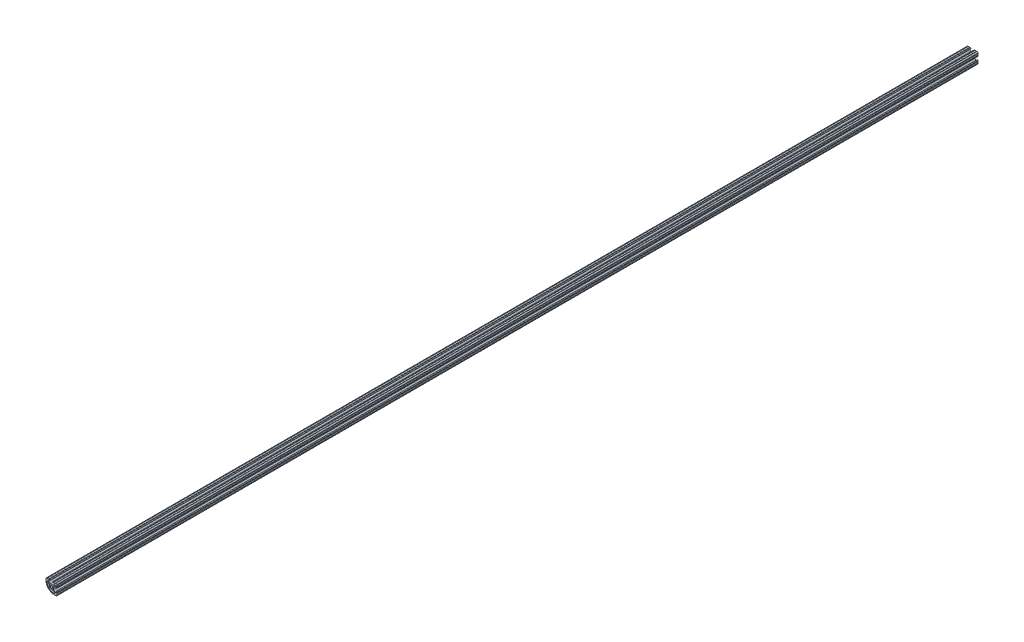
SolidWorks part; units mm, degrees
ref_plane "Front Plane" through (0, 0, 0) normal (0, 0, 1) x (1, 0, 0)
ref_plane "Top Plane" through (0, 0, 0) normal (0, 1, 0) x (1, 0, 0)
ref_plane "Right Plane" through (0, 0, 0) normal (1, 0, 0) x (0, 0, -1)
sketch "Sketch1" plane through (0, 0, 0) normal (0, 0, 1) x (1, 0, 0)
  line L0 (-5.2807, 3.6664) -> (-8.6034, 6.9891)
  line L2 (-12.7, 9.5758) -> (-12.7, 6.35)
  line L17 (1.6698, 4.4958) -> (-1.6698, 4.4958)
  line L18 (-3.9149, 5.4257) -> (-7.0932, 8.604)
  line L19 (-6.3119, 10.4902) -> (-4.3561, 10.4902)
  line L20 (-4.3561, 12.7) -> (-5.334, 12.7)
  line L21 (-6.35, 12.7) -> (-9.5758, 12.7)
  line L22 (-12.7, -12.7) -> (12.7, 12.7) construction
  line L23 (0, 12.7) -> (0, -12.7) construction
  line L24 (-12.7, -12.7) -> (12.7, -12.7) construction
  line L25 (-7.1204, -7.1204) -> (-1.5408, -12.7) construction
  line L26 (-12.0825, 12.0825) -> (0, 0) construction
  line L27 (3.9149, 5.4257) -> (7.0932, 8.604)
  line L28 (6.3119, 10.4902) -> (4.3561, 10.4902)
  line L29 (4.3561, 12.7) -> (5.334, 12.7)
  line L30 (6.35, 12.7) -> (9.5758, 12.7)
  arc A0 (1.8411, 1.8411) -> (-1.8411, -1.8411) centre (0, 0) ccw
  arc A2 (-10.4895, 6.1978) -> (-5.5578, -5.5578) centre (6.35, 6.35) ccw
  arc A3 (-8.6034, 6.9891) -> (-10.4895, 6.1978) centre (-9.3847, 6.2078) ccw
  arc A4 (-4.4059, 0.8321) -> (-5.2807, 3.6664) centre (-7.5257, 1.4213) ccw
  arc A5 (-4.4059, 0.8321) -> (-3.1705, -3.1705) centre (0, 0) ccw
  arc A7 (-10.5918, 12.7) -> (-12.7, 10.5918) centre (-10.5918, 10.5918) ccw
  arc A8 (-12.7, 9.5758) -> (-12.7, 10.5918) centre (-12.7, 10.0838) ccw
  arc A9 (-12.7, 6.35) -> (-11.886, 0.8407) centre (6.35, 6.35) ccw
  arc A10 (-11.5663, -0.1236) -> (-11.886, 0.8407) centre (-11.7326, 0.3564) ccw
  arc A11 (-11.5663, -0.1236) -> (-10.4403, -2.6494) centre (6.35, 6.35) ccw
  arc A12 (-9.9367, -3.5317) -> (-10.4403, -2.6494) centre (-10.1943, -3.0939) ccw
  arc A13 (-9.9367, -3.5317) -> (-7.1204, -7.1204) centre (6.35, 6.35) ccw
  arc A36 (-3.9149, 5.4257) -> (-1.6698, 4.4958) centre (-1.6698, 7.6708) ccw
  arc A37 (-6.3119, 10.4902) -> (-7.0932, 8.604) centre (-6.3119, 9.3853) ccw
  arc A38 (-4.3561, 10.4902) -> (-4.3561, 12.7) centre (-4.3561, 11.5951) ccw
  arc A39 (-6.35, 12.7) -> (-5.334, 12.7) centre (-5.842, 12.7) ccw
  arc A40 (-10.5918, 12.7) -> (-9.5758, 12.7) centre (-10.0838, 12.7) ccw
  arc A41 (3.9149, 5.4257) -> (1.6698, 4.4958) centre (1.6698, 7.6708) cw
  arc A42 (6.3119, 10.4902) -> (7.0932, 8.604) centre (6.3119, 9.3853) cw
  arc A43 (4.3561, 10.4902) -> (4.3561, 12.7) centre (4.3561, 11.5951) cw
  arc A44 (6.35, 12.7) -> (5.334, 12.7) centre (5.842, 12.7) cw
  arc A45 (10.5918, 12.7) -> (9.5758, 12.7) centre (10.0838, 12.7) cw
  arc A46 (10.5918, 12.7) -> (12.0825, 12.0825) centre (10.5918, 10.5918) cw
  point P17 (0, 4.4958)
  dimension "Raidus" = 19.05
  dimension "D3" = 0.508
  dimension "D11" = 2.1082
  dimension "D13" = 3.175
  dimension "D14" = 2.6037
  dimension "D15" = 4.4838
  dimension "Rail Height" = 25.4
  dimension "D2" = 45
  dimension "D4" = 10.1943
  dimension "D7" = 1.5408
  dimension "D5" = 11.7326
  dimension "D8" = 2.2098
  dimension "TSLot Width" = 6.5024
  dimension "D9" = 14.8336
  dimension "D10" = 8.2042
  dimension "D12" = 2.2098
  dimension "Rail Width" = 25.4
  dimension "D6" = 2.2098
sketch "Sketch2" plane through (0, 0, 0) normal (1, 0, 0) x (0, 0, -1)
  line L0 (-1250, 0) -> (1250, 0)
  point P2 (-1211.9, 0)
  point P4 (1211.9, 0)
  dimension "Length" = 2500
  dimension "D1" = 38.1
  dimension "D2" = 38.1
sketch "Sketch3" plane through (0, 0, 0) normal (0, 0, 1) x (1, 0, 0)
  line L0 (6.35, 12.7) -> (9.5758, 12.7) construction
  line L1 (4.3561, 12.7) -> (5.334, 12.7) construction
  line L2 (6.3119, 10.4902) -> (4.3561, 10.4902) construction
  line L3 (3.9149, 5.4257) -> (7.0932, 8.604) construction
  line L4 (1.6698, 4.4958) -> (-1.6698, 4.4958) construction
  line L5 (-3.9149, 5.4257) -> (-7.0932, 8.604) construction
  line L6 (-6.3119, 10.4902) -> (-4.3561, 10.4902) construction
  line L7 (-4.3561, 12.7) -> (-5.334, 12.7) construction
  line L8 (-6.35, 12.7) -> (-9.5758, 12.7) construction
  line L9 (-12.7, 9.5758) -> (-12.7, 6.35) construction
  line L10 (-5.2807, 3.6664) -> (-8.6034, 6.9891) construction
  line L22 (6.35, 12.7) -> (9.5758, 12.7)
  line L59 (4.3561, 12.7) -> (5.334, 12.7)
  line L60 (6.3119, 10.4902) -> (4.3561, 10.4902)
  line L61 (3.9149, 5.4257) -> (7.0932, 8.604)
  line L62 (1.6698, 4.4958) -> (-1.6698, 4.4958)
  line L63 (-3.9149, 5.4257) -> (-7.0932, 8.604)
  line L64 (-6.3119, 10.4902) -> (-4.3561, 10.4902)
  line L65 (-4.3561, 12.7) -> (-5.334, 12.7)
  line L66 (-6.35, 12.7) -> (-9.5758, 12.7)
  line L67 (-12.7, 9.5758) -> (-12.7, 6.35)
  line L68 (-5.2807, 3.6664) -> (-8.6034, 6.9891)
  line L69 (-3.1705, -3.1705) -> (-1.8411, -1.8411)
  line L70 (-7.1204, -7.1204) -> (-5.5578, -5.5578)
  line L71 (1.8411, 1.8411) -> (12.0825, 12.0825)
  arc A0 (1.8411, 1.8411) -> (-1.8411, -1.8411) centre (0, 0) ccw construction
  arc A1 (12.0825, 12.0825) -> (10.5918, 12.7) centre (10.5918, 10.5918) ccw construction
  arc A2 (9.5758, 12.7) -> (10.5918, 12.7) centre (10.0838, 12.7) ccw construction
  arc A3 (5.334, 12.7) -> (6.35, 12.7) centre (5.842, 12.7) ccw construction
  arc A4 (4.3561, 12.7) -> (4.3561, 10.4902) centre (4.3561, 11.5951) ccw construction
  arc A5 (7.0932, 8.604) -> (6.3119, 10.4902) centre (6.3119, 9.3853) ccw construction
  arc A6 (1.6698, 4.4958) -> (3.9149, 5.4257) centre (1.6698, 7.6708) ccw construction
  arc A7 (-3.9149, 5.4257) -> (-1.6698, 4.4958) centre (-1.6698, 7.6708) ccw construction
  arc A8 (-6.3119, 10.4902) -> (-7.0932, 8.604) centre (-6.3119, 9.3853) ccw construction
  arc A9 (-4.3561, 10.4902) -> (-4.3561, 12.7) centre (-4.3561, 11.5951) ccw construction
  arc A10 (-6.35, 12.7) -> (-5.334, 12.7) centre (-5.842, 12.7) ccw construction
  arc A11 (-10.5918, 12.7) -> (-9.5758, 12.7) centre (-10.0838, 12.7) ccw construction
  arc A12 (-10.5918, 12.7) -> (-12.7, 10.5918) centre (-10.5918, 10.5918) ccw construction
  arc A13 (-12.7, 9.5758) -> (-12.7, 10.5918) centre (-12.7, 10.0838) ccw construction
  arc A14 (-12.7, 6.35) -> (-11.886, 0.8407) centre (6.35, 6.35) ccw construction
  arc A15 (-11.5663, -0.1236) -> (-11.886, 0.8407) centre (-11.7326, 0.3564) ccw construction
  arc A16 (-11.5663, -0.1236) -> (-10.4403, -2.6494) centre (6.35, 6.35) ccw construction
  arc A17 (-9.9367, -3.5317) -> (-10.4403, -2.6494) centre (-10.1943, -3.0939) ccw construction
  arc A18 (-9.9367, -3.5317) -> (-7.1204, -7.1204) centre (6.35, 6.35) ccw construction
  arc A19 (-10.4895, 6.1978) -> (-5.5578, -5.5578) centre (6.35, 6.35) ccw construction
  arc A20 (-8.6034, 6.9891) -> (-10.4895, 6.1978) centre (-9.3847, 6.2078) ccw construction
  arc A21 (-4.4059, 0.8321) -> (-5.2807, 3.6664) centre (-7.5257, 1.4213) ccw construction
  arc A22 (-4.4059, 0.8321) -> (-3.1705, -3.1705) centre (0, 0) ccw construction
  arc A110 (1.8411, 1.8411) -> (-1.8411, -1.8411) centre (0, 0) ccw
  arc A111 (12.0825, 12.0825) -> (10.5918, 12.7) centre (10.5918, 10.5918) ccw
  arc A112 (9.5758, 12.7) -> (10.5918, 12.7) centre (10.0838, 12.7) ccw
  arc A113 (5.334, 12.7) -> (6.35, 12.7) centre (5.842, 12.7) ccw
  arc A114 (4.3561, 12.7) -> (4.3561, 10.4902) centre (4.3561, 11.5951) ccw
  arc A115 (7.0932, 8.604) -> (6.3119, 10.4902) centre (6.3119, 9.3853) ccw
  arc A116 (1.6698, 4.4958) -> (3.9149, 5.4257) centre (1.6698, 7.6708) ccw
  arc A117 (-3.9149, 5.4257) -> (-1.6698, 4.4958) centre (-1.6698, 7.6708) ccw
  arc A118 (-6.3119, 10.4902) -> (-7.0932, 8.604) centre (-6.3119, 9.3853) ccw
  arc A119 (-4.3561, 10.4902) -> (-4.3561, 12.7) centre (-4.3561, 11.5951) ccw
  arc A120 (-6.35, 12.7) -> (-5.334, 12.7) centre (-5.842, 12.7) ccw
  arc A121 (-10.5918, 12.7) -> (-9.5758, 12.7) centre (-10.0838, 12.7) ccw
  arc A122 (-10.5918, 12.7) -> (-12.7, 10.5918) centre (-10.5918, 10.5918) ccw
  arc A123 (-12.7, 9.5758) -> (-12.7, 10.5918) centre (-12.7, 10.0838) ccw
  arc A124 (-12.7, 6.35) -> (-11.886, 0.8407) centre (6.35, 6.35) ccw
  arc A125 (-11.5663, -0.1236) -> (-11.886, 0.8407) centre (-11.7326, 0.3564) ccw
  arc A126 (-11.5663, -0.1236) -> (-10.4403, -2.6494) centre (6.35, 6.35) ccw
  arc A127 (-9.9367, -3.5317) -> (-10.4403, -2.6494) centre (-10.1943, -3.0939) ccw
  arc A128 (-9.9367, -3.5317) -> (-7.1204, -7.1204) centre (6.35, 6.35) ccw
  arc A129 (-10.4895, 6.1978) -> (-5.5578, -5.5578) centre (6.35, 6.35) ccw
  arc A130 (-8.6034, 6.9891) -> (-10.4895, 6.1978) centre (-9.3847, 6.2078) ccw
  arc A131 (-4.4059, 0.8321) -> (-5.2807, 3.6664) centre (-7.5257, 1.4213) ccw
  arc A132 (-4.4059, 0.8321) -> (-3.1705, -3.1705) centre (0, 0) ccw
extrude "Boss-Extrude1" add sketch "Sketch3" along normal mid plane 2500
mirror "Mirror1" about plane through (1.8411, 1.8411, 1250) normal (-0.7071, 0.7071, 0) of bodies 104
ref_plane "Contact Plane 1" through (-3.2512, 0, 0) normal (1, 0, 0) x (0, 0, -1)
ref_plane "Contact Plane 2" through (0, -3.2512, 0) normal (0, 1, 0) x (1, 0, 0)
sketch "Sketch4" plane through (0, 0, 1250) normal (0, 0, 1) x (1, 0, 0)
  circle A0 centre (0, 0) radius 22.75
extrude "Cut-Extrude1" cut sketch "Sketch4" against normal blind 361.95
sketch "Sketch6" [suppressed] plane through (0, 0, 1032.83) normal (0, 0, -1) x (-1, 0, 0)
  point P0 (0, 0)
sketch "Sketch7" [suppressed] plane through (0, 0, 1032.83) normal (0, 0, 1) x (1, 0, 0)
  circle A0 centre (0, 0) radius 25.4
  dimension "D1" = 50.8
equation "\"D3@Sketch1\" = \"Rail Height@Sketch1\" * 0.0200in"
equation "\"D4@Sketch1\" = \"Rail Height@Sketch1\" * 0.4013523in"
equation "\"D7@Sketch1\" = \"Rail Height@Sketch1\" * 0.06066017in"
equation "\"D8@Sketch1\" = \"Rail Height@Sketch1\" * 0.0870in"
equation "\"D9@Sketch1\" = \"Rail Height@Sketch1\" * 0.584"
equation "\"D10@Sketch1\" = \"Rail Height@Sketch1\" * 0.323"
equation "\"D11@Sketch1\" = \"Rail Height@Sketch1\" * 0.0830in"
equation "\"D12@Sketch1\" = \"Rail Height@Sketch1\" * 0.087"
equation "\"D13@Sketch1\" = \"Rail Height@Sketch1\" * 0.1250in"
equation "\"D14@Sketch1\" = \"Rail Height@Sketch1\" * 0.10250886in"
equation "\"D15@Sketch1\" = \"Rail Height@Sketch1\" * 0.17652717in"
equation "\"D5@Sketch1\"=\"Rail Height@Sketch1\"*0.46191253in"
equation "\"D1@Boss-Extrude1\" = \"Length@Sketch2\""
equation "\"D6@Sketch1\"=\"Rail Height@Sketch1\"*0.0870in"
equation "\"D2@Sketch2\"=\"D1@Sketch2\""
